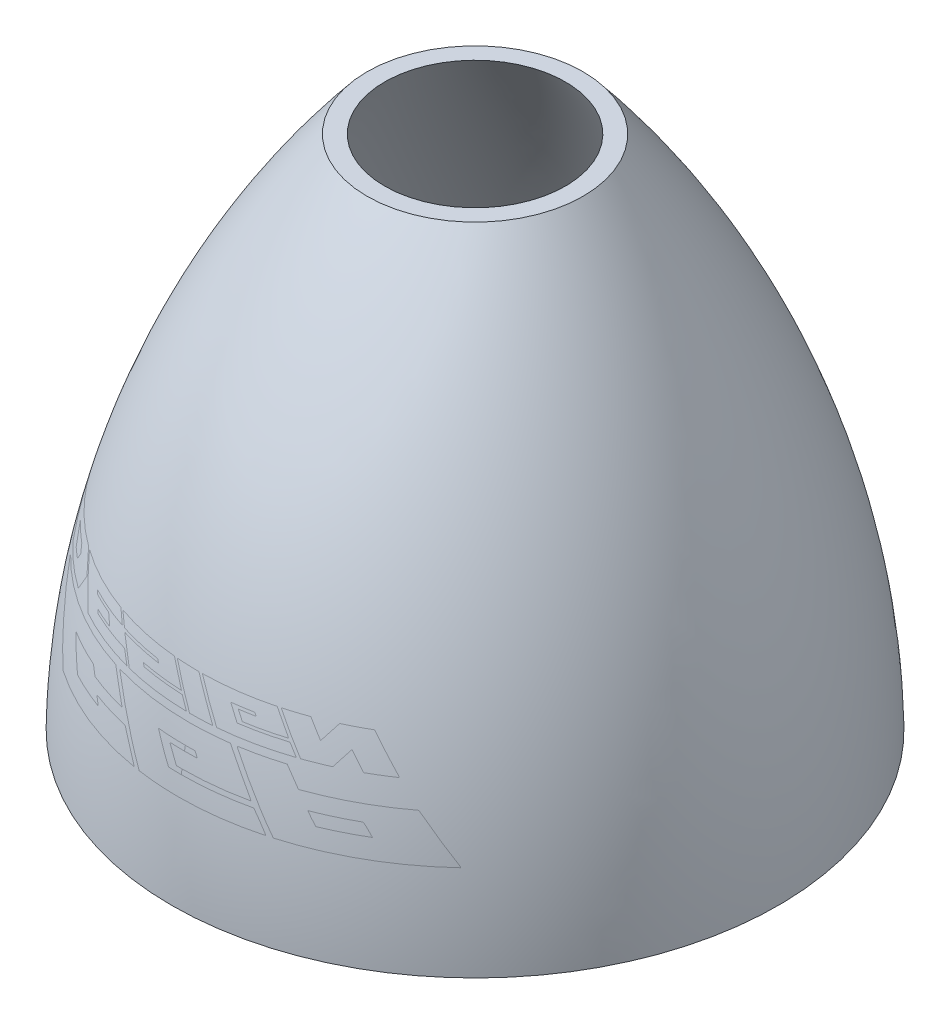
SolidWorks part; units mm, degrees
ref_plane "Front Plane" through (0, 0, 0) normal (0, 0, 1) x (1, 0, 0)
ref_plane "Top Plane" through (0, 0, 0) normal (0, 1, 0) x (1, 0, 0)
ref_plane "Right Plane" through (0, 0, 0) normal (1, 0, 0) x (0, 0, -1)
sketch "Sketch1" plane through (0, 0, 0) normal (0, 0, 1) x (1, 0, 0)
  line L0 (0, 618.9038) -> (0, -618.9038) construction
  line L1 (0, -618.9038) -> (630.0173, -618.9038) construction
  line L2 (0, -618.9038) -> (582.9115, -618.9038) construction
  line L3 (582.9115, -618.9038) -> (630.0173, -618.9038)
  line L4 (187.7022, 453.7913) -> (224.25, 453.7913)
  spline S0 degree 3 poles (630.0173, -618.9038) (623.6962, -228.9541) (470.6355, 152.4962) (224.25, 453.7913) knots 0 0 0 0 1 1 1 1
  spline S1 degree 3 poles (582.9115, -618.9038) (580.9143, -428.7642) (484.9544, -51.6243) (302.4173, 292.5292) (187.7022, 453.7913) knots 0 0 0 0 0.487151 1 1 1 1
revolve "Revolve1" add sketch "Sketch1" angle 360 about L0
ref_plane "Plane1" through (0, 0, -720) normal (0, 0, 1) x (1, 0, 0)
sketch "Sketch2" plane through (0, 0, -720) normal (0, 0, 1) x (1, 0, 0)
  line L0 (555.9827, -307.5068) -> (-630.0173, -307.5068) construction
  line L1 (-630.0173, -225.5068) -> (449.9827, -225.5068) construction
  text T0 "CGP" font "WWE Raw" height in points 500
  text T1 "design" font "WWE Raw" height in points 275
  dimension "D1" = 1186
  dimension "D2" = 1080
  dimension "D3" = 82
split line "Split Line3"
